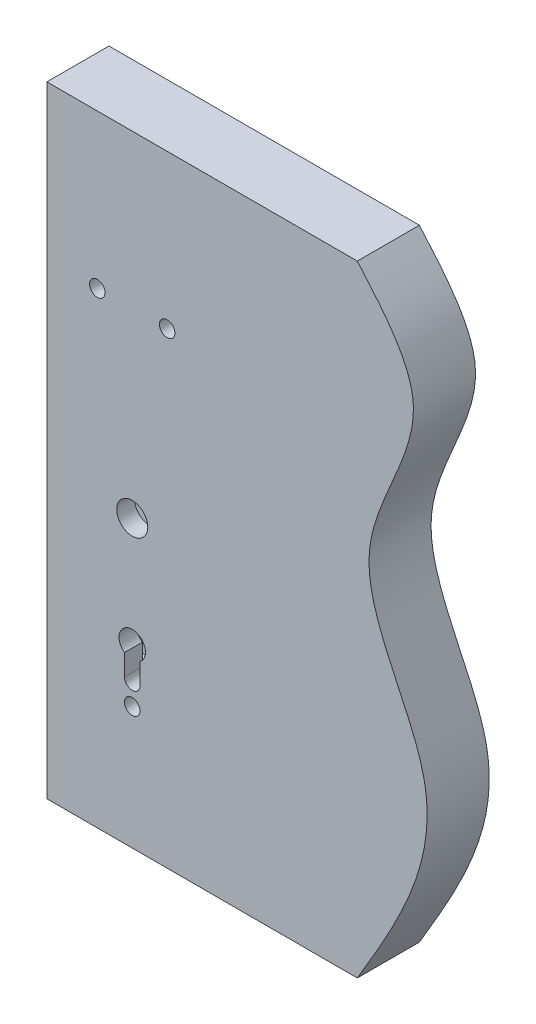
SolidWorks part; units mm, degrees
material "Chêne"
ref_plane "Face" through (0, 0, 0) normal (0, 0, 1) x (1, 0, 0)
ref_plane "Dessus" through (0, 0, 0) normal (0, 1, 0) x (1, 0, 0)
ref_plane "Droite" through (0, 0, 0) normal (1, 0, 0) x (0, 0, -1)
sketch "Esquisse1" plane through (0, 0, 0) normal (0, 0, 1) x (1, 0, 0)
  line L0 (0, 0) -> (0, 57.0464) construction
  line L1 (-150, 200) -> (50, 200)
  line L2 (-150, 200) -> (-150, -200)
  line L3 (-150, -200) -> (50, -200)
  line L5 (0, 0) -> (65.7907, 0) construction
  spline S0 degree 3 poles (50, 200) (66.8796, 180.5626) (108.794, 132.2966) (27.2783, 35.2366) (123.4738, -75.9938) (75.8926, -156.2995) (50, -200) knots 0 0 0 0 0.163804 0.406749 0.677167 1 1 1 1
  dimension "D1" = 200
  dimension "D2" = 400
extrude "Extrusion1" add sketch "Esquisse1" along normal mid plane 40
sketch "Esquisse2" plane through (-150, 0, 0) normal (-1, 0, 0) x (0, 0, 1)
  line L0 (0, 0) -> (0, 41.3685) construction
  line L1 (-11, 80) -> (11, 80)
  line L2 (-11, 80) -> (-11, -150)
  line L3 (-11, -150) -> (11, -150)
  line L4 (11, 80) -> (11, -150)
  line L5 (0, 41.3685) -> (0, 0) construction
  line L6 (0, 0) -> (40.4435, 0) construction
  line L7 (20, 200) -> (-20, 200) construction
  point P7 (0, 200)
  dimension "D1" = 230
  dimension "D2" = 22
  dimension "D3" = 120
extrude "Enlèv. mat.-Extru.1" cut sketch "Esquisse2" against normal blind 3
sketch "Esquisse3" plane through (37.1525, -36.3213, 0) normal (0, 0, 1) x (0, 1, 0)
  line L0 (236.3213, 187.1525) -> (-163.6787, 187.1525) construction
  line L1 (-80.1787, 184.1525) -> (82.8213, 184.1525)
  line L2 (-80.1787, 184.1525) -> (-80.1787, 107.1525)
  line L3 (-80.1787, 107.1525) -> (82.8213, 107.1525)
  line L4 (82.8213, 184.1525) -> (82.8213, 107.1525)
  line L7 (36.3213, 37.1525) -> (36.3213, -86.8563) construction
  line L8 (236.3213, -12.8475) -> (236.3213, 187.1525) construction
  line L9 (-163.6787, 187.1525) -> (-163.6787, -12.8475) construction
  dimension "D1" = 163
  dimension "D2" = 77
  dimension "D3" = 3
  dimension "D4" = 153.5
extrude "Enlèv. mat.-Extru.2" cut sketch "Esquisse3" against normal mid plane 17
sketch "Esquisse4" plane through (0, 0, 20) normal (0, 0, 1) x (1, 0, 0)
  line L1 (-150, 200) -> (-150, -200) construction
  line L2 (50, 200) -> (-150, 200) construction
  line L3 (-95, -16) -> (-95, 156.6738) construction
  circle A0 centre (-95, -16) radius 10
  circle A1 centre (-117.5, 101) radius 5
  circle A2 centre (-95, -121) radius 5
  circle A3 centre (-72.5, 101) radius 5
  dimension "D3" = 20
  dimension "D4" = 10
  dimension "D5" = 10
  dimension "D9" = 10
  dimension "D1" = 55
  dimension "D2" = 216
  dimension "D6" = 117
  dimension "D7" = 105
  dimension "D8" = 22.5
extrude "Enlèv. mat.-Extru.3" cut sketch "Esquisse4" against normal through all
sketch "Esquisse5" plane through (0, 0, -20) normal (0, 0, -1) x (-1, 0, 0)
  line L0 (90, -104.8326) -> (90, -107) construction
  line L1 (100, -107) -> (100, -93.3739) construction
  line L2 (90, -93.3739) -> (90, -107)
  line L3 (100, -107) -> (100, -93.3739)
  arc A0 (90, -107) -> (100, -107) centre (95, -107) ccw construction
  arc A1 (93.0139, -78.2353) -> (90, -93.3739) centre (95, -86.5) ccw construction
  arc A2 (100, -93.3739) -> (96.9861, -78.2353) centre (95, -86.5) ccw construction
  arc A3 (90, -107) -> (100, -107) centre (95, -107) ccw
  arc A4 (93.0139, -78.2353) -> (90, -93.3739) centre (95, -86.5) ccw
  arc A5 (100, -93.3739) -> (93.0139, -78.2353) centre (95, -86.5) ccw
extrude "Enlèv. mat.-Extru.4" cut sketch "Esquisse5" against normal through all
